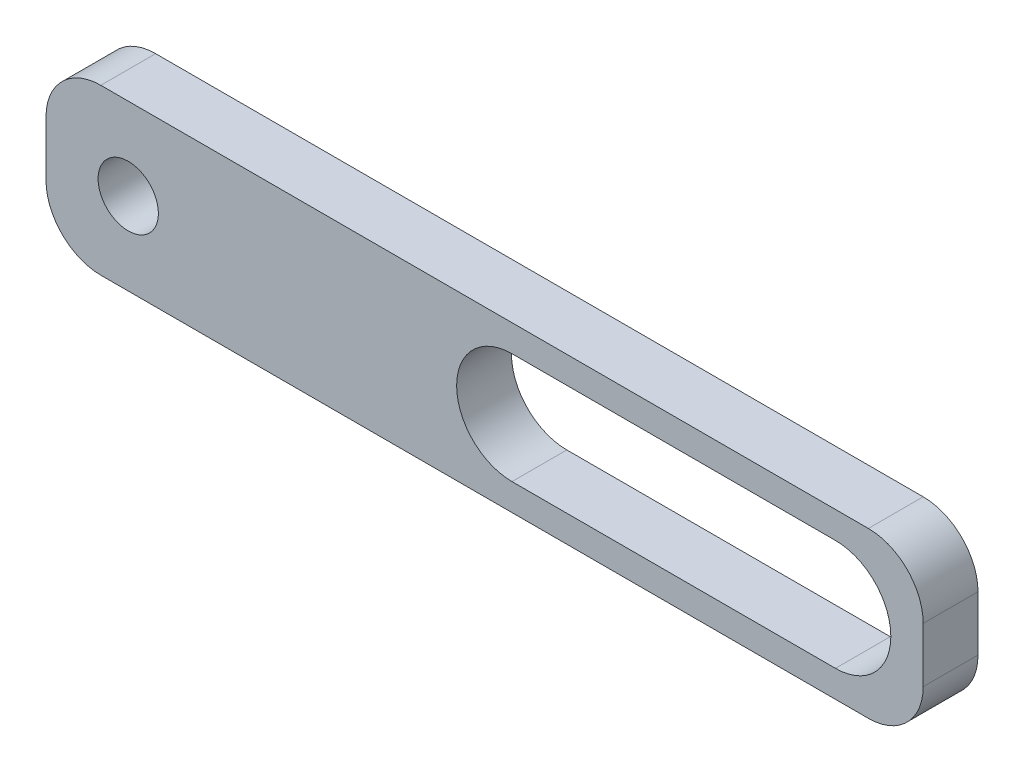
SolidWorks part; units mm, degrees
ref_plane "Alzado" through (0, 0, 0) normal (0, 0, 1) x (1, 0, 0)
ref_plane "Planta" through (0, 0, 0) normal (0, 1, 0) x (1, 0, 0)
ref_plane "Vista lateral" through (0, 0, 0) normal (1, 0, 0) x (0, 0, -1)
sketch "Sketch1" plane through (0, 0, 0) normal (0, 0, 1) x (1, 0, 0)
  line L0 (0, 5) -> (0, 10)
  line L1 (5, 15) -> (75, 15)
  line L2 (80, 10) -> (80, 5)
  line L3 (75, 0) -> (5, 0)
  line L4 (42.5, 7.5) -> (72, 7.5) construction
  line L5 (42.5, 12.55) -> (72, 12.55)
  line L6 (42.5, 2.45) -> (72, 2.45)
  arc A0 (5, 0) -> (0, 5) centre (5, 5) cw
  arc A1 (75, 0) -> (80, 5) centre (75, 5) ccw
  arc A2 (80, 10) -> (75, 15) centre (75, 10) ccw
  arc A3 (0, 10) -> (5, 15) centre (5, 10) cw
  arc A4 (42.5, 12.55) -> (42.5, 2.45) centre (42.5, 7.5) ccw
  arc A5 (72, 2.45) -> (72, 12.55) centre (72, 7.5) ccw
  circle A6 centre (7.5, 7.5) radius 2.75
  point P7 (0, 0)
  point P16 (57.25, 7.5)
  dimension "D1" = 5
  dimension "D7" = 42.5
  dimension "D5" = 5.05
  dimension "D9" = 5.5
  dimension "D2" = 15
  dimension "D3" = 80
  dimension "D4" = 8
  dimension "D6" = 2.45
  dimension "D8" = 7.5
extrude "Boss-Extrude1" add sketch "Sketch1" along normal blind 5
